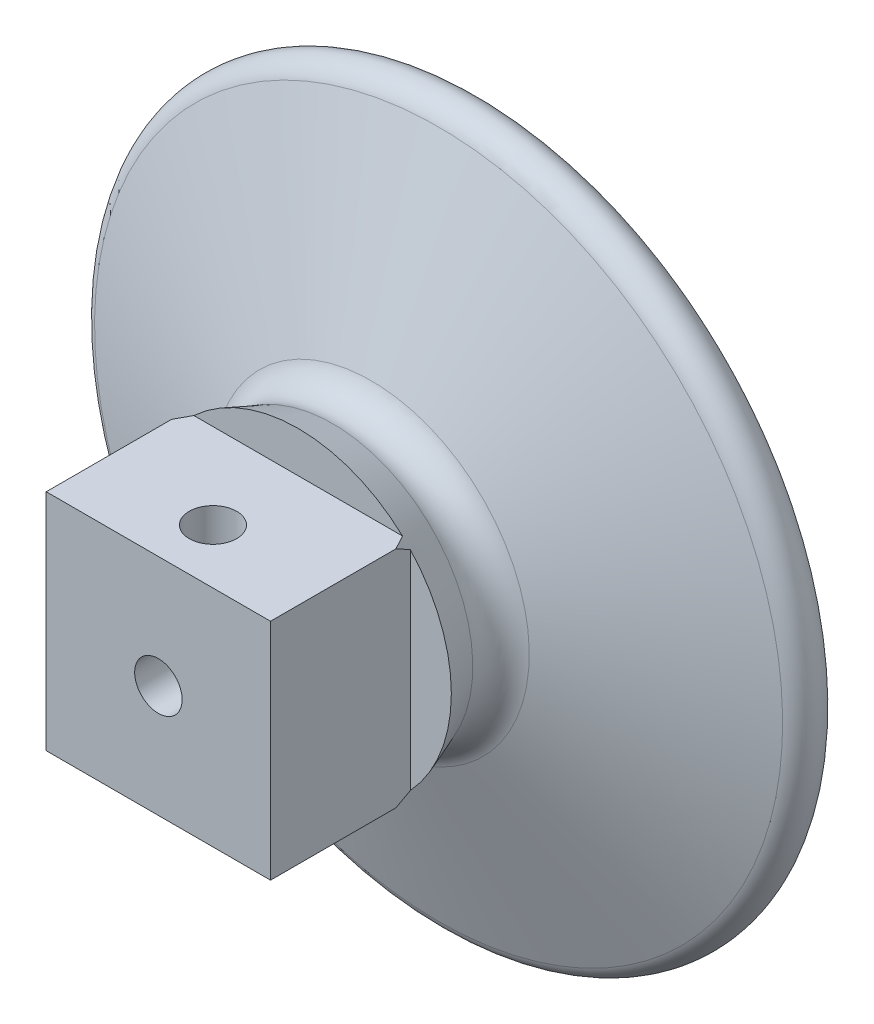
SolidWorks part; units mm, degrees
ref_plane "Front Plane" through (0, 0, 0) normal (0, 0, 1) x (1, 0, 0)
ref_plane "Top Plane" through (0, 0, 0) normal (0, 1, 0) x (1, 0, 0)
ref_plane "Right Plane" through (0, 0, 0) normal (1, 0, 0) x (0, 0, -1)
sketch "Sketch2" plane through (0, 0, 0) normal (1, 0, 0) x (0, 0, -1)
  line L0 (-1049.4378, 0) -> (-15.34, 0) construction
  line L1 (8, 9.378) -> (-13.2524, 17.372)
  line L3 (-9.34, 0) -> (17.5, 0)
  line L5 (15.0896, 23.0107) -> (10.5846, 10.5691)
  line L6 (9.1687, 24) -> (-23.7199, 24) construction
  line L7 (-13.9565, 17.5) -> (-25.8605, 17.5) construction
  line L8 (3.956, 9.25) -> (-6.7768, 9.25) construction
  line L9 (-15.34, 0) -> (-9.34, 0) construction
  line L10 (-9.34, 0) -> (50000, 0) construction
  line L11 (-15.34, 0) -> (-9.34, 0) construction
  line L12 (-15.34, 14.0557) -> (-15.34, 0) construction
  line L13 (-15.9565, 15.5) -> (-15.9565, 21.7755) construction
  line L14 (17.5, 21.382) -> (17.5, 0)
  line L15 (18, 22.5) -> (18, 34.1993) construction
  arc A0 (17.5, 21.382) -> (15.0896, 23.0107) centre (16.5, 22.5) ccw
  arc A1 (-13.2524, 17.372) -> (-15.34, 14.0557) centre (-13.9565, 15.5) ccw
  arc A2 (8, 9.378) -> (10.5846, 10.5691) centre (8.7041, 11.25) ccw
  arc A4 (-15.34, 14.0557) -> (-9.34, 0) centre (-28.8035, 0) cw
  dimension "D1" = 1.5
  dimension "D2" = 2
  dimension "D6" = 2
  dimension "D9" = 6
  dimension "D3" = 18
  dimension "D4" = 24
  dimension "D5" = 17.5
  dimension "D7" = 9.25
  dimension "D8" = 33.34
  dimension "D10" = 10
  dimension "D11" = 1
revolve "Revolve1" add sketch "Sketch2" angle 360 about L10
sketch "Sketch6" plane through (0, 0, 0) normal (0, 1, 0) x (1, 0, 0)
  line L0 (-15.0038, -6.9565) -> (-14.9951, -6.9598)
  line L1 (-15.0038, -6.9565) -> (-17.372, -13.2524)
  line L2 (-14.9951, -6.9598) -> (-17.362, -13.2524)
  line L4 (-9.378, 8) -> (-17.372, -13.2524) construction
  line L5 (-15.5, -15.9565) -> (15.5, -15.9565) construction
  line L6 (-17.362, -13.2524) -> (-17.372, -13.2524)
  line L8 (0, 0) -> (0, -6.5458) construction
  line L9 (17.372, -13.2524) -> (-17.372, -13.2524) construction
  dimension "D1" = 9
  dimension "D2" = 0.01
revolve "Cut-Revolve1" cut sketch "Sketch6" angle 360 about L8
sketch "Sketch3" plane through (0, 0, -17.5) normal (0, 0, -1) x (-1, 0, 0)
  circle A0 centre (0, 0) radius 1.5875
  dimension "D1" = 3.175
extrude "Cut-Extrude1" cut sketch "Sketch3" against normal through all both and the other way through all
sketch "Sketch4" plane through (0, 0, 0) normal (0, 0, 1) x (1, 0, 0)
  line L0 (0, 0) -> (0, 47.0796) construction
  line L1 (0, 24) -> (-14.7149, 24) construction
  line L2 (0, 1.5875) -> (5.5, 1.5875)
  line L3 (0, 1.5875) -> (0, 28.5)
  line L4 (4.5, 28.5) -> (5.5, 28.5)
  line L5 (5.5, 1.5875) -> (5.5, 28.5)
  line L6 (0, 28.5) -> (4.5, 28.5) construction
  line L7 (0, 28.5) -> (4.5, 28.5) construction
  line L8 (0, 28.5) -> (0, 44.5)
  line L9 (0, 44.5) -> (4, 44.5)
  line L10 (4.5, 28.5) -> (4.5, 32.5) construction
  line L11 (4.5, 28.5) -> (4, 32.5)
  line L12 (4, 32.5) -> (4.5, 32.5)
  line L13 (4, 36.5) -> (4.5, 36.5)
  line L14 (4.5, 32.5) -> (4, 36.5)
  line L15 (4, 40.5) -> (4.5, 40.5)
  line L16 (4.5, 36.5) -> (4, 40.5)
  line L17 (4, 44.5) -> (4.5, 44.5) construction
  line L18 (4.5, 40.5) -> (4, 44.5)
  line L19 (4.5, 40.5) -> (4.5, 44.5) construction
  line L20 (4, 44.5) -> (4.5, 44.5) construction
  line L21 (4.5, 36.5) -> (4.5, 40.5) construction
  line L22 (4.5, 32.5) -> (4.5, 36.5) construction
  circle A0 centre (0, 0) radius 24 construction
  circle A1 centre (0, 0) radius 1.5875 construction
  dimension "D1" = 11
  dimension "D2" = 4.5
  dimension "D3" = 4.5
  dimension "D5" = 16
  dimension "D6" = 8
  dimension "D4" = 4
revolve "Revolve2" add sketch "Sketch4" angle 360 about L0
sketch "Sketch5" plane through (0, 44.5, 0) normal (0, 1, 0) x (1, 0, 0)
  circle A0 centre (0, 0) radius 1.5875
  dimension "D1" = 3.175
extrude "Cut-Extrude2" cut sketch "Sketch5" against normal up to surface and the other way through all up to face at (1.5875, 0, 9.4048)
sketch "Sketch7" plane through (0, 0, 0) normal (0, 0, 1) x (1, 0, 0)
  line L1 (-7.5, -7.5) -> (7.5, -7.5)
  line L2 (-7.5, -7.5) -> (-7.5, 7.5)
  line L3 (-7.5, 7.5) -> (7.5, 7.5)
  line L4 (7.5, -7.5) -> (7.5, 7.5)
  line L5 (-7.5, -7.5) -> (7.5, 7.5) construction
  line L6 (-7.5, 7.5) -> (7.5, -7.5) construction
  line L7 (-36.8208, -47.5838) -> (36.8208, -47.5838)
  line L8 (-36.8208, -47.5838) -> (-36.8208, 47.5838)
  line L9 (-36.8208, 47.5838) -> (36.8208, 47.5838)
  line L10 (36.8208, -47.5838) -> (36.8208, 47.5838)
  line L11 (-36.8208, -47.5838) -> (36.8208, 47.5838) construction
  line L12 (-36.8208, 47.5838) -> (36.8208, -47.5838) construction
  point P0 (0, 0)
  point P7 (0, 0)
  dimension "D1" = 15
extrude "Cut-Extrude3" cut sketch "Sketch7" along normal blind 30 from offset 5.7 contours L7 L10 L9 L8 L4 L1 L2 L3 offset against normal yes
sketch "Sketch8" plane through (0, 7.5, 0) normal (0, 1, 0) x (1, 0, 0)
  line L1 (-8.577, -3.65) -> (14.0437, -3.65)
  line L2 (-8.577, -3.65) -> (-8.577, -14.6603)
  line L3 (-8.577, -14.6603) -> (14.0437, -14.6603)
  line L4 (14.0437, -3.65) -> (14.0437, -14.6603)
  line L5 (-6.9766, 5.7) -> (6.9766, 5.7) construction
  point P4 (0, -0.65)
  dimension "D1" = 6.35
  dimension "D2" = 3
extrude "Cut-Extrude4" cut sketch "Sketch8" against normal blind 19
